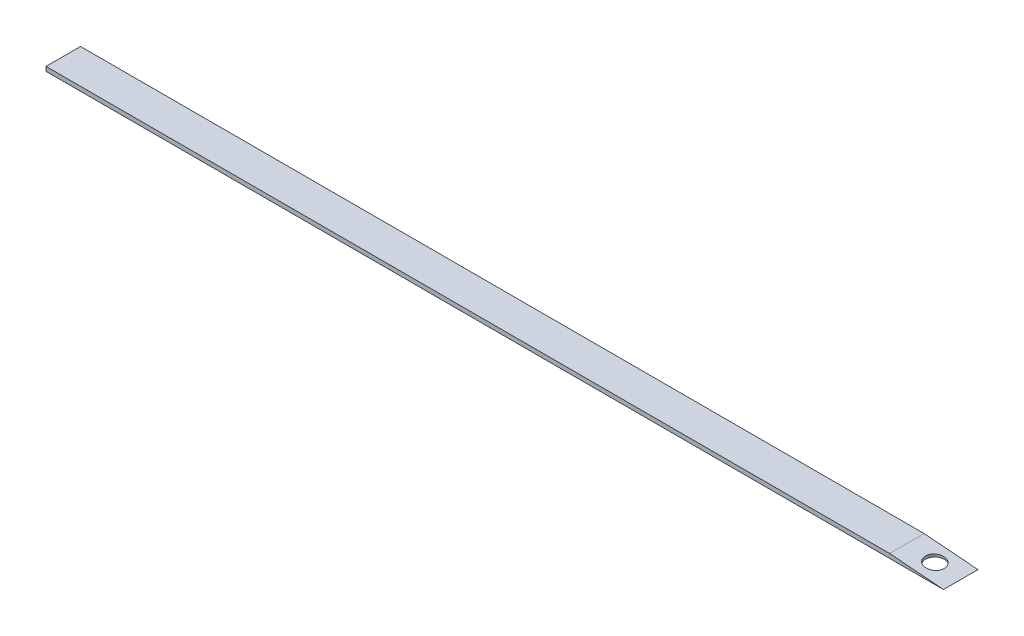
SolidWorks part; units mm, degrees
ref_plane "Front Plane" through (0, 0, 0) normal (0, 0, 1) x (1, 0, 0)
ref_plane "Top Plane" through (0, 0, 0) normal (0, 1, 0) x (1, 0, 0)
ref_plane "Right Plane" through (0, 0, 0) normal (1, 0, 0) x (0, 0, -1)
sketch "Sketch1" plane through (0, 0, 0) normal (0, 1, 0) x (1, 0, 0)
  line L1 (330.2, -6.35) -> (0, -6.35)
  line L2 (330.2, -6.35) -> (330.2, 6.35)
  line L3 (330.2, 6.35) -> (0, 6.35)
  line L4 (0, -6.35) -> (0, 6.35)
  circle A0 centre (320.675, 0) radius 3.429
  dimension "D1" = 320.675
  dimension "D2" = 330.2
extrude "Extrude1" add sketch "Sketch1" along normal blind 1.5875
sketch "Sketch2" plane through (0, 0, 0) normal (0, 0, 1) x (1, 0, 0)
  line L0 (330.2, 0) -> (330.2, 2.264)
  line L1 (330.2, 2.264) -> (301.9545, 2.264)
  line L2 (301.9545, 2.264) -> (330.2, 0)
extrude "Cut-Extrude2" cut sketch "Sketch2" against normal through all and the other way through all
